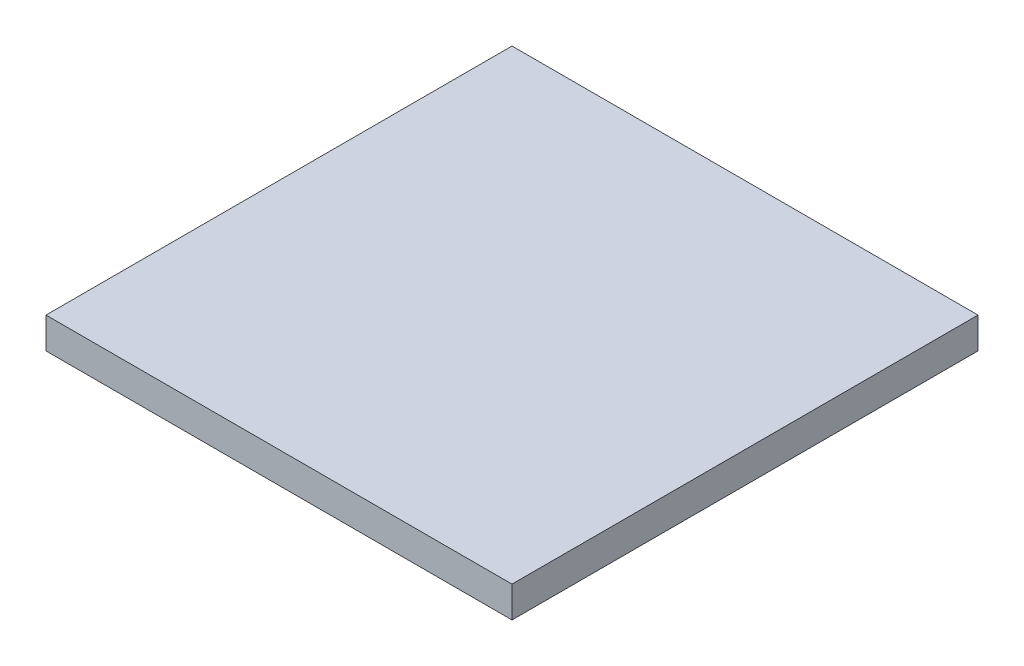
SolidWorks part; units mm, degrees
ref_plane "Front Plane" through (0, 0, 0) normal (0, 0, 1) x (1, 0, 0)
ref_plane "Top Plane" through (0, 0, 0) normal (0, 1, 0) x (1, 0, 0)
ref_plane "Right Plane" through (0, 0, 0) normal (1, 0, 0) x (0, 0, -1)
sketch "Sketch1" plane through (0, 0, 0) normal (0, 0, 1) x (1, 0, 0)
  line L1 (0, 0) -> (381, 0)
  line L2 (0, 0) -> (0, 25.4)
  line L3 (0, 25.4) -> (381, 25.4)
  line L4 (381, 0) -> (381, 25.4)
  dimension "D1" = 25.4
  dimension "D2" = 381
extrude "Boss-Extrude1" add sketch "Sketch1" along normal blind 381
